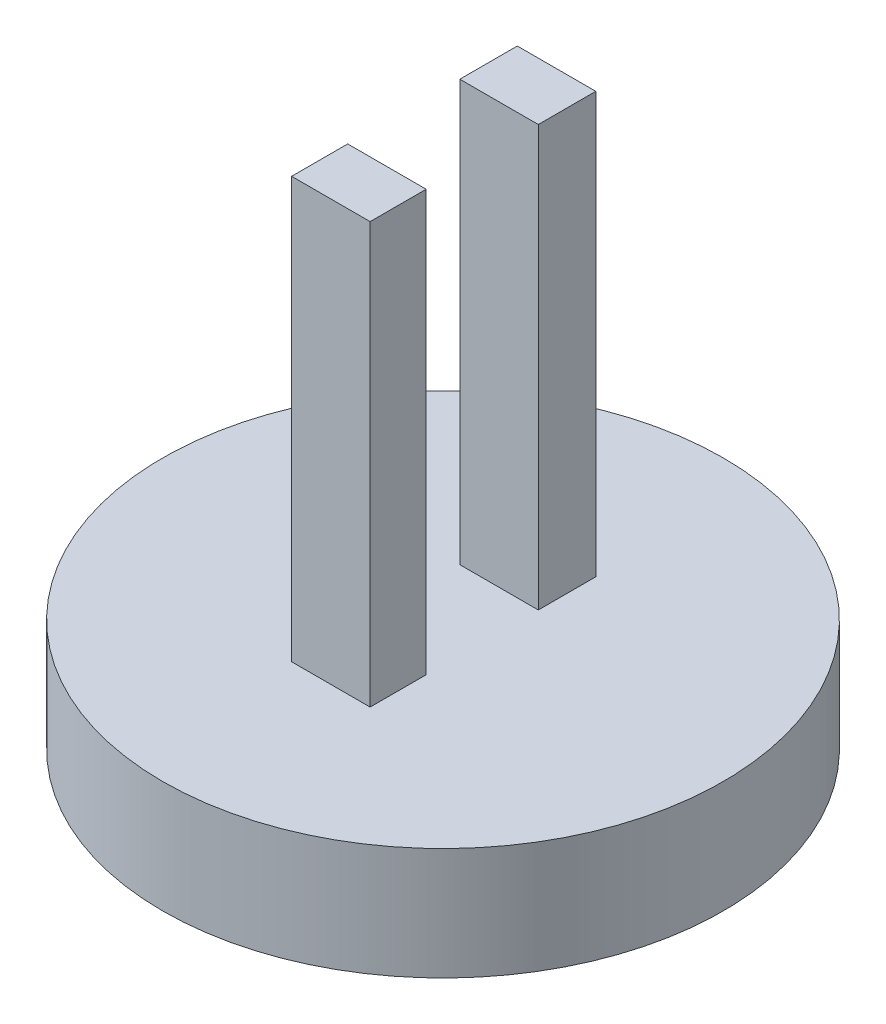
SolidWorks part; units mm, degrees
ref_plane "Front Plane" through (0, 0, 0) normal (0, 0, 1) x (1, 0, 0)
ref_plane "Top Plane" through (0, 0, 0) normal (0, 1, 0) x (1, 0, 0)
ref_plane "Right Plane" through (0, 0, 0) normal (1, 0, 0) x (0, 0, -1)
sketch "Sketch1" plane through (0, 0, 0) normal (0, 1, 0) x (1, 0, 0)
  circle A0 centre (0, 0) radius 12.7
extrude "Boss-Extrude1" add sketch "Sketch1" along normal blind 5.08
sketch "Sketch2" plane through (0, 5.08, 0) normal (0, 1, 0) x (1, 0, 0)
  line L9 (-1.778, 2.54) -> (1.778, 2.54)
  line L10 (-1.778, 2.54) -> (-1.778, 5.1447)
  line L11 (-1.778, 5.1447) -> (1.778, 5.1447)
  line L12 (1.778, 2.54) -> (1.778, 5.1447)
  line L17 (-1.778, -2.54) -> (1.778, -2.54)
  line L18 (-1.778, -2.54) -> (-1.778, -5.08)
  line L19 (-1.778, -5.08) -> (1.778, -5.08)
  line L20 (1.778, -2.54) -> (1.778, -5.08)
  point P4 (0, 0)
  point P7 (0, 0)
  point P11 (0, 0)
  point P12 (0, 0)
  dimension "D1" = 2.54
  dimension "D3" = 3.556
  dimension "D4" = 2.6047
  dimension "D2" = 1.778
  dimension "D5" = 2.54
  dimension "D7" = 3.556
  dimension "D8" = 2.54
  dimension "D6" = 1.778
extrude "Boss-Extrude2" add sketch "Sketch2" along normal blind 19.05 contours L11 L12 L9 L10 | L17 L20 L19 L18
